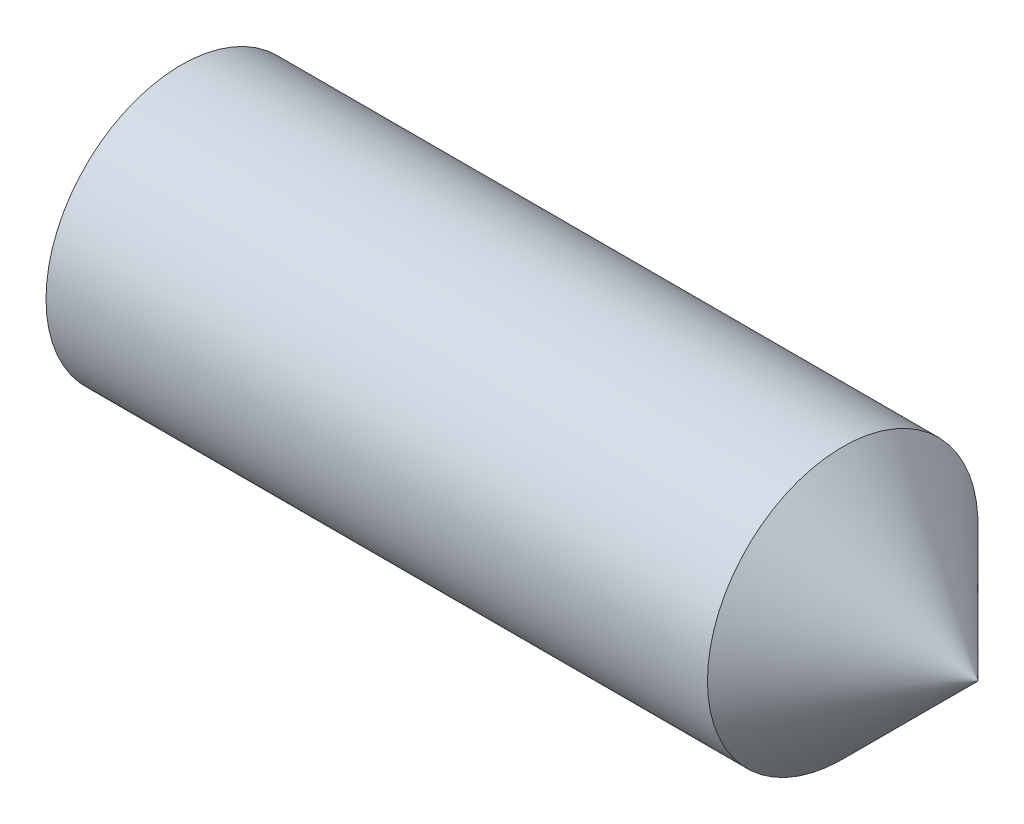
SolidWorks part; units mm, degrees
ref_plane "Plane1" through (0, 0, 0) normal (0, 0, 1) x (1, 0, 0)
ref_plane "Plane2" through (0, 0, 0) normal (0, 1, 0) x (1, 0, 0)
ref_plane "Plane3" through (0, 0, 0) normal (1, 0, 0) x (0, 0, -1)
sketch "BodySke" plane through (0, 0, 0) normal (0, 0, 1) x (1, 0, 0)
  line L0 (0, 0) -> (0, 1.61)
  line L1 (0, 1.61) -> (0.2252, 2)
  line L2 (0.2252, 2) -> (10.005, 2)
  line L3 (10.005, 2) -> (12, 0.005)
  line L4 (12, 0) -> (0, 0)
  line L5 (-12.7, 0) -> (88.9, 0) construction
  line L6 (12, 0.005) -> (12, 0)
  line L7 (12, 0.005) -> (12, 9.53) construction
  line L8 (0, -1.61) -> (0.2252, -2) construction
  line L9 (0.7, 15.875) -> (0.7, -3.175) construction
  line L10 (10.005, -2) -> (12, -0.005) construction
  dimension "Cone_ang" = 90
  dimension "Length" = 12
  dimension "Diameter" = 4
  dimension "Drive_ch_ang" = 60
  dimension "Minor_dia" = 3.22
  dimension "Tip_dia" = 0.01
  dimension "Advance" = 0.7
revolve "BaseBody" add sketch "BodySke" angle 360 about L5
cosmetic thread "ThreadCosmetic" [suppressed] parameters "Thread_minor"=3.22
sketch "Sketch2" plane through (0, 0, 0) normal (-1, 0, 0) x (0, 0, 1)
  line L0 (0.5774, 1) -> (-0.5774, 1)
  line L1 (-0.5774, 1) -> (-1.1547, 0)
  line L2 (0.5774, 1) -> (1.1547, 0)
  line L3 (0.5774, -1) -> (1.1547, 0)
  line L4 (0.5774, -1) -> (-0.5774, -1)
  line L5 (-0.5774, -1) -> (-1.1547, 0)
  dimension "Hex_size" = 2
  dimension "D2" = 1
  dimension "D3" = 1
extrude "Hex" cut sketch "Sketch2" against normal blind 2.5
sketch "ThdSchSke" [suppressed] plane through (0, 0, 0) normal (0, 0, 1) x (1, 0, 0)
  line L0 (0.9515, -10.352) -> (-0.2025, -12)
  line L1 (0.9515, -10.352) -> (2.1054, -12)
  line L2 (2.1054, -12) -> (2.1054, -15)
  line L3 (-3.175, 0) -> (5.1513, 0) construction
  line L5 (2.1054, -15) -> (-0.2025, -15)
  line L6 (-0.2025, -15) -> (-0.2025, -12)
  line L8 (0.9515, 12) -> (0.9515, -12) construction
  dimension "Thread_minor" = 3.22
  dimension "Diameter" = 4
  dimension "SideAngle" = 55
  dimension "VeeAngle" = 70
  dimension "Overcut" = 5
revolve "ThreadSchematic" [suppressed] cut sketch "ThdSchSke" angle 360 about L3
pattern_linear "ThdSchPat" [suppressed]
equation "\"D2@Sketch2\" = \"Hex_size@Sketch2\" / 2"
equation "\"D3@Sketch2\" = \"Hex_size@Sketch2\" / 2"
equation "\"Thread_minor@ThreadCosmetic\" = \"Minor_dia@BodySke\""
equation "\"Thread_minor@ThdSchSke\" = \"Thread_minor@ThreadCosmetic\""
equation "\"Diameter@ThdSchSke\" = \"Diameter@BodySke\""
equation "\"Overcut@ThdSchSke\" = \"Diameter@BodySke\" * 1.25"
equation "\"Num_threads@ThdSchPat\" = int( (\"Length@BodySke\" - ( ( ( \"Diameter@BodySke\" - \"Minor_dia@BodySke\" ) * 0.5 ) / tan( \"Drive_ch_ang@BodySke\" * 0.017453292 ) ) - ( ( ( \"Diameter@BodySke\" - \"Tip_dia@BodySke\" ) * 0.5 ) / tan( \"Cone_ang@BodySke\" / 2.0 * 0.017453292 ) ) ) / \"Advance@BodySke\" + 0.999 )  + 1"
equation "\"Advance@ThdSchPat\" = (\"Length@BodySke\" - ( ( ( \"Diameter@BodySke\" - \"Minor_dia@BodySke\" ) * 0.5 ) / tan( \"Drive_ch_ang@BodySke\" * 0.017453292 ) ) - ( ( ( \"Diameter@BodySke\" - \"Tip_dia@BodySke\" ) * 0.5 ) / tan( \"Cone_ang@BodySke\" / 2.0 * 0.017453292 ) ) ) /  (\"Num_threads@ThdSchPat\" - 1) 'relax it"
equation "' \"Num_threads@ThdSchPat\" = \"Num_threads@ThdSchPat\" - sgn( \"Num_threads@ThdSchPat\" - 1) '---chamfered tips only---"
